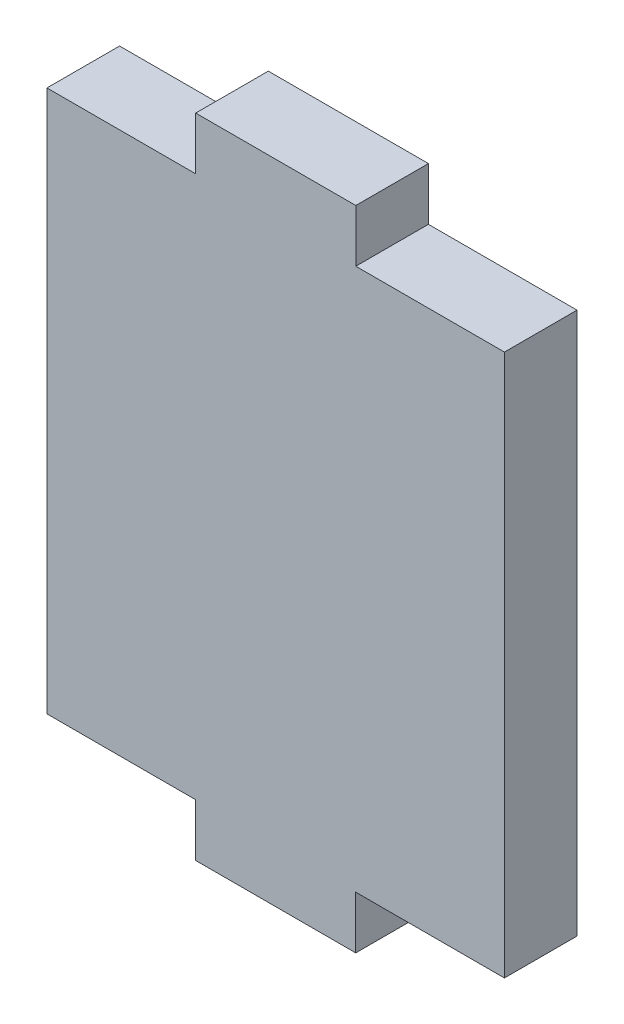
SolidWorks part; units mm, degrees
ref_plane "Front Plane" through (0, 0, 0) normal (0, 0, 1) x (1, 0, 0)
ref_plane "Top Plane" through (0, 0, 0) normal (0, 1, 0) x (1, 0, 0)
ref_plane "Right Plane" through (0, 0, 0) normal (1, 0, 0) x (0, 0, -1)
sketch "Sketch1" plane through (0, 0, 0) normal (0, 0, 1) x (1, 0, 0)
  line L1 (0, 0) -> (20, 0)
  line L2 (0, 0) -> (0, 23.7)
  line L3 (0, 23.7) -> (20, 23.7)
  line L4 (20, 0) -> (20, 23.7)
extrude "Boss-Extrude1" add sketch "Sketch1" along normal blind 3.175
sketch "Sketch2" plane through (0, 0, 3.175) normal (0, 0, 1) x (1, 0, 0)
  line L0 (20, 23.7) -> (0, 23.7) construction
  line L1 (6.5021, 23.7) -> (13.5021, 23.7)
  line L2 (6.5021, 23.7) -> (6.5021, 26)
  line L3 (6.5021, 26) -> (13.5021, 26)
  line L4 (13.5021, 23.7) -> (13.5021, 26)
  line L5 (0, 0) -> (20, 0) construction
  line L6 (6.5, 0) -> (13.5, 0)
  line L7 (6.5, 0) -> (6.5, -2.3)
  line L8 (6.5, -2.3) -> (13.5, -2.3)
  line L9 (13.5, 0) -> (13.5, -2.3)
  line L10 (0, 23.7) -> (0, 0) construction
  line L11 (20, 0) -> (20, 23.7) construction
  dimension "D1" = 7
  dimension "D2" = 2.3
  dimension "D3" = 2.3
  dimension "D4" = 7
  dimension "D5" = 6.5021
  dimension "D6" = 6.4979
  dimension "D7" = 6.5
extrude "Boss-Extrude2" add sketch "Sketch2" against normal blind 3.175
